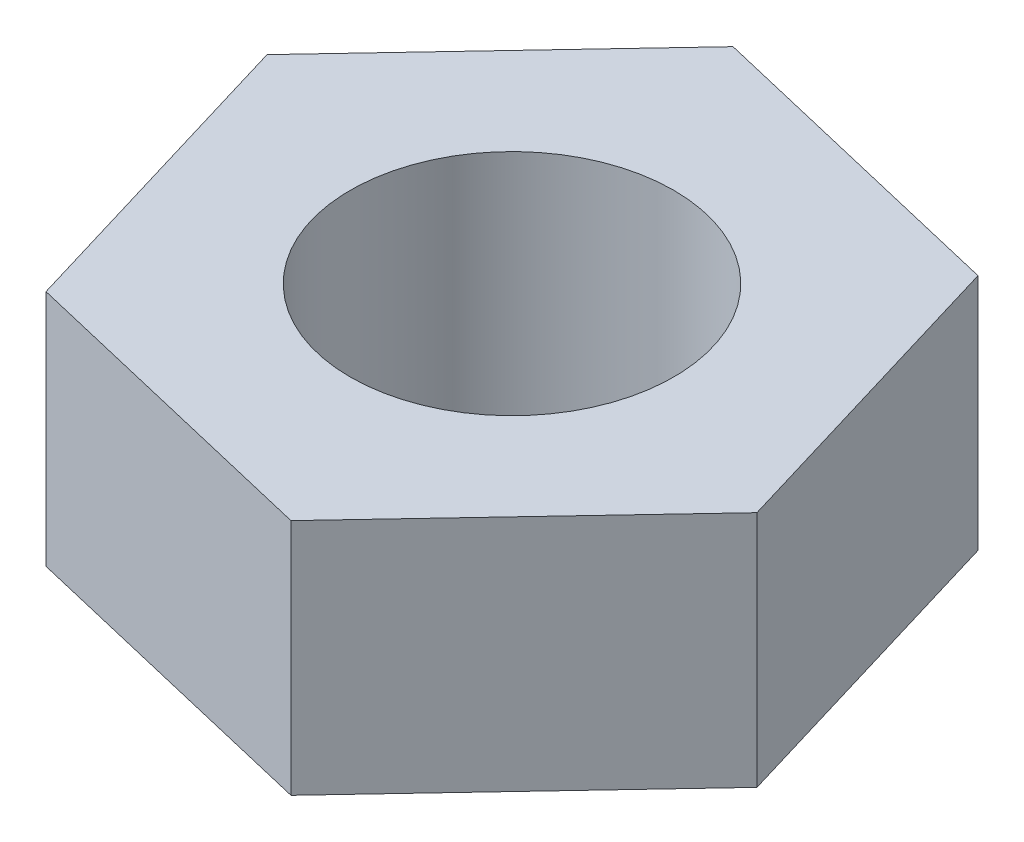
SolidWorks part; units mm, degrees
ref_plane "前视基准面" through (0, 0, 0) normal (0, 0, 1) x (1, 0, 0)
ref_plane "上视基准面" through (0, 0, 0) normal (0, 1, 0) x (1, 0, 0)
ref_plane "右视基准面" through (0, 0, 0) normal (1, 0, 0) x (0, 0, -1)
sketch "草图1" plane through (0, 0, 0) normal (0, 1, 0) x (1, 0, 0)
  line L1 (2.9862, -9.954) -> (10.1135, -2.3909)
  line L2 (10.1135, -2.3909) -> (7.1273, 7.5631)
  line L3 (7.1273, 7.5631) -> (-2.9862, 9.954)
  line L4 (-2.9862, 9.954) -> (-10.1135, 2.3909)
  line L5 (-10.1135, 2.3909) -> (-7.1273, -7.5631)
  line L6 (-7.1273, -7.5631) -> (2.9862, -9.954)
  circle A0 centre (0, 0) radius 9 construction
  dimension "D1" = 18
extrude "凸台-拉伸1" add sketch "草图1" along normal blind 7.5
sketch "草图5" plane through (0, 7.5, 0) normal (0, 1, 0) x (1, 0, 0)
  line L0 (-10.1135, 2.3909) -> (10.1135, -2.3909)
  line L1 (10.1135, -2.3909) -> (7.1273, 7.5631)
  line L2 (7.1273, 7.5631) -> (-7.1273, -7.5631)
hole_wizard "M12 螺纹孔1" positions "3D草图3" profile "草图6" tap size "M12" standard "GB"
sketch3d "3D草图3"
  line L0 (-10.1135, 7.5, -2.3909) -> (10.1135, 7.5, 2.3909) construction
  point P0 (0, 7.5, 0)
  point P4 (0, 0, 0)
  point P7 (0, 0, 0)
  dimension "D1" = 0
sketch "草图6" plane through (0, 0, 0) normal (1, 0, 0) x (0, 0, -1)
  line L0 (0, 0) -> (0, 32.3144)
  line L1 (0, 32.3144) -> (5.1, 29.25)
  line L2 (5.1, 29.25) -> (5.1, 0)
  line L5 (5.1, 0) -> (0, 0)
  line L10 (0, 32.3144) -> (-5.1, 29.25) construction
  line L11 (0, -6.35) -> (0, 107.95) construction
  dimension "螺纹孔钻头直径" = 10.2
  dimension "螺纹孔钻头深度" = 29.25
  dimension "导头角度" = 118
cosmetic thread "孔螺蚊线1"
cosmetic thread "孔螺蚊线2"
cosmetic thread "孔螺蚊线3"
